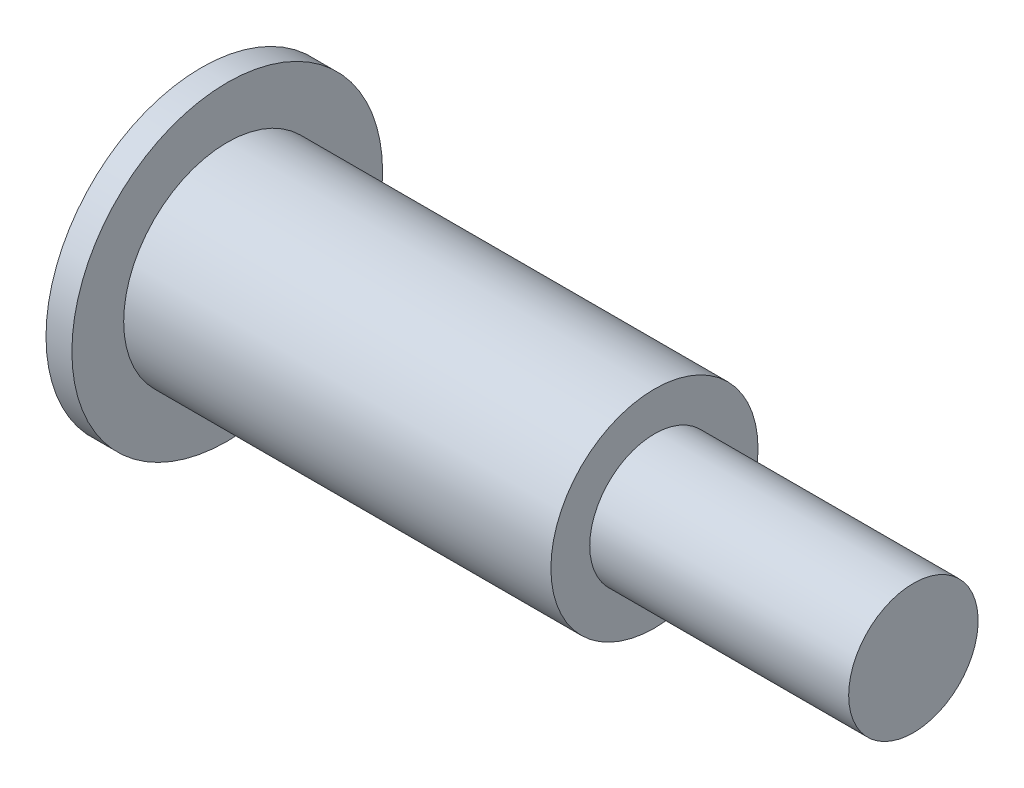
SolidWorks part; units mm, degrees
ref_plane "Plan de face" through (0, 0, 0) normal (0, 0, 1) x (1, 0, 0)
ref_plane "Plan de dessus" through (0, 0, 0) normal (0, 1, 0) x (1, 0, 0)
ref_plane "Plan de droite" through (0, 0, 0) normal (1, 0, 0) x (0, 0, -1)
sketch "Esquisse1" plane through (0, 0, 0) normal (0, 0, 1) x (1, 0, 0)
  line L0 (0, 0) -> (22.3998, 0) construction
  line L1 (0, 0) -> (0, 6)
  line L2 (0, 6) -> (1, 6)
  line L3 (1, 6) -> (1, 4)
  line L4 (1, 4) -> (17.5, 4)
  line L5 (17.5, 4) -> (17.5, 2.5)
  line L6 (17.5, 2.5) -> (27.5, 2.5)
  line L7 (27.5, 2.5) -> (27.5, 0)
  line L8 (27.5, 0) -> (0, 0)
  dimension "D1" = 1.5
  dimension "D2" = 16.5
  dimension "D3" = 10
revolve "Révolution1" add sketch "Esquisse1" angle 360 about L0
